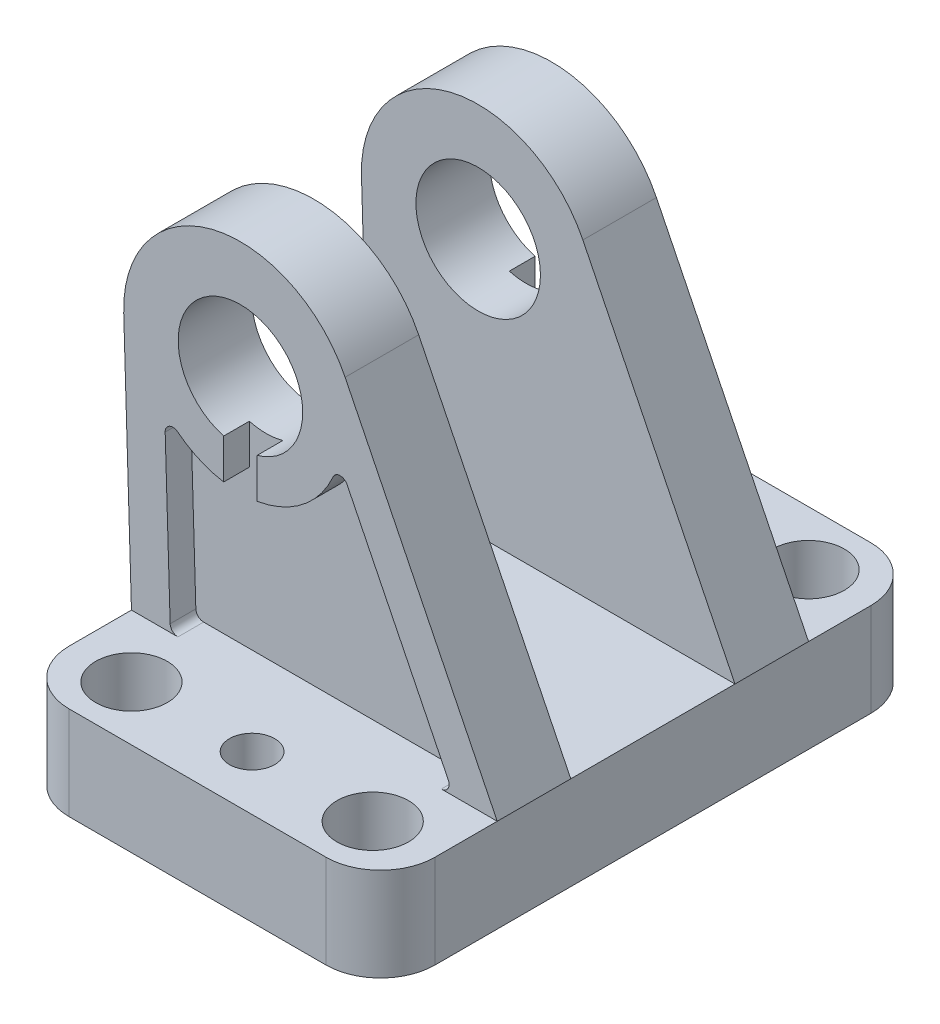
SolidWorks part; units mm, degrees
ref_plane "Front Plane" through (0, 0, 0) normal (0, 0, 1) x (1, 0, 0)
ref_plane "Top Plane" through (0, 0, 0) normal (0, 1, 0) x (1, 0, 0)
ref_plane "Right Plane" through (0, 0, 0) normal (1, 0, 0) x (0, 0, -1)
ref_plane "Plane1" through (0, 0, 0) normal (0, 1, 0) x (1, 0, 0)
sketch "Sketch1" plane through (0, 0, 0) normal (0, 1, 0) x (1, 0, 0)
  line L0 (-16.5, -35) -> (16.5, -35)
  line L1 (23.5, -28) -> (23.5, 28)
  line L2 (16.5, 35) -> (-16.5, 35)
  line L3 (-23.5, 28) -> (-23.5, -28)
  arc A0 (-23.5, -28) -> (-16.5, -35) centre (-16.5, -28) ccw
  arc A1 (16.5, -35) -> (23.5, -28) centre (16.5, -28) ccw
  arc A2 (23.5, 28) -> (16.5, 35) centre (16.5, 28) ccw
  arc A3 (-16.5, 35) -> (-23.5, 28) centre (-16.5, 28) ccw
  circle A4 centre (15.5, 28) radius 4.6
  circle A5 centre (15.5, -28) radius 4.6
  circle A6 centre (0, 28) radius 2.9
  circle A7 centre (0, -28) radius 2.9
  circle A8 centre (-15.5, 28) radius 4.6
  circle A9 centre (-15.5, -28) radius 4.6
extrude "Boss-Extrude1" add sketch "Sketch1" along normal blind 12
ref_plane "Plane2" through (0, 0, 0) normal (0, 1, 0) x (1, 0, 0)
sketch "Sketch2" plane through (0, 0, 0) normal (0, 1, 0) x (1, 0, 0)
  line L0 (-8.006, -23) -> (8.006, -23)
  line L1 (18.5, -18.6106) -> (18.5, 18.6106)
  line L2 (8.006, 23) -> (-8.006, 23)
  line L3 (-18.5, 18.6106) -> (-18.5, -18.6106)
  arc A0 (-18.5, -18.6106) -> (-17.2917, -19.5887) centre (-17.5, -18.6106) ccw
  arc A1 (-17.2917, -19.5887) -> (-8.7866, -22.625) centre (-15.5, -28) cw
  arc A2 (-8.7866, -22.625) -> (-8.006, -23) centre (-8.006, -22) ccw
  arc A3 (8.006, -23) -> (8.7866, -22.625) centre (8.006, -22) ccw
  arc A4 (8.7866, -22.625) -> (17.2917, -19.5887) centre (15.5, -28) cw
  arc A5 (17.2917, -19.5887) -> (18.5, -18.6106) centre (17.5, -18.6106) ccw
  arc A6 (18.5, 18.6106) -> (17.2917, 19.5887) centre (17.5, 18.6106) ccw
  arc A7 (17.2917, 19.5887) -> (8.7866, 22.625) centre (15.5, 28) cw
  arc A8 (8.7866, 22.625) -> (8.006, 23) centre (8.006, 22) ccw
  arc A9 (-8.006, 23) -> (-8.7866, 22.625) centre (-8.006, 22) ccw
  arc A10 (-8.7866, 22.625) -> (-17.2917, 19.5887) centre (-15.5, 28) cw
  arc A11 (-17.2917, 19.5887) -> (-18.5, 18.6106) centre (-17.5, 18.6106) ccw
extrude "Cut-Extrude1" cut sketch "Sketch2" along normal blind 6
ref_plane "Plane3" through (0, 0, 20) normal (0, 0, 1) x (1, 0, 0)
sketch "Sketch3" plane through (0, 0, 20) normal (0, 0, 1) x (1, 0, 0)
  line L0 (-24.493, 44.5425) -> (-23.5, 12)
  line L1 (-23.5, 12) -> (23.5, 12)
  line L2 (23.5, 12) -> (3.9529, 51.6347)
  arc A0 (3.9529, 51.6347) -> (-24.493, 44.5425) centre (-9.5, 45) ccw
  circle A1 centre (-9.5, 45) radius 8
extrude "Boss-Extrude2" add sketch "Sketch3" against normal blind 9.45
ref_plane "Plane4" through (0, 0, 20) normal (0, 0, 1) x (1, 0, 0)
sketch "Sketch4" plane through (0, 0, 20) normal (0, 0, 1) x (1, 0, 0)
  line L0 (-19.1683, 33.9762) -> (-18.5273, 12.9695)
  line L1 (-17.5277, 12) -> (16.3168, 12)
  line L2 (17.2137, 13.4423) -> (4.2119, 39.8054)
  arc A0 (-17.5495, 34.7919) -> (-19.1683, 33.9762) centre (-18.1687, 34.0067) ccw
  arc A1 (-18.5273, 12.9695) -> (-17.5277, 12) centre (-17.5277, 13) ccw
  arc A2 (16.3168, 12) -> (17.2137, 13.4423) centre (16.3168, 13) ccw
  arc A3 (4.2119, 39.8054) -> (2.3997, 39.7657) centre (3.315, 39.3631) ccw
  arc A4 (2.3997, 39.7657) -> (-17.5495, 34.7919) centre (-9.5, 45) cw
extrude "Cut-Extrude2" cut sketch "Sketch4" against normal blind 3.3
ref_plane "Plane5" through (0, 0, -20) normal (0, 0, 1) x (1, 0, 0)
sketch "Sketch5" plane through (0, 0, -20) normal (0, 0, 1) x (1, 0, 0)
  line L0 (-24.493, 44.5425) -> (-23.5, 12)
  line L1 (-23.5, 12) -> (23.5, 12)
  line L2 (23.5, 12) -> (3.9529, 51.6347)
  arc A0 (3.9529, 51.6347) -> (-24.493, 44.5425) centre (-9.5, 45) ccw
  circle A1 centre (-9.5, 45) radius 8
extrude "Boss-Extrude3" add sketch "Sketch5" along normal blind 9.45
ref_plane "Plane6" through (0, 0, -20) normal (0, 0, 1) x (1, 0, 0)
sketch "Sketch6" plane through (0, 0, -20) normal (0, 0, 1) x (1, 0, 0)
  line L0 (-19.1683, 33.9762) -> (-18.5273, 12.9695)
  line L1 (-17.5277, 12) -> (16.3168, 12)
  line L2 (17.2137, 13.4423) -> (4.2119, 39.8054)
  arc A0 (-17.5495, 34.7919) -> (-19.1683, 33.9762) centre (-18.1687, 34.0067) ccw
  arc A1 (-18.5273, 12.9695) -> (-17.5277, 12) centre (-17.5277, 13) ccw
  arc A2 (16.3168, 12) -> (17.2137, 13.4423) centre (16.3168, 13) ccw
  arc A3 (4.2119, 39.8054) -> (2.3997, 39.7657) centre (3.315, 39.3631) ccw
  arc A4 (2.3997, 39.7657) -> (-17.5495, 34.7919) centre (-9.5, 45) cw
extrude "Cut-Extrude3" cut sketch "Sketch6" along normal blind 3.3
ref_plane "Plane7" through (0, 0, 20) normal (0, 0, 1) x (1, 0, 0)
sketch "Sketch7" plane through (0, 0, 20) normal (0, 0, 1) x (1, 0, 0)
  line L0 (-7.35, 30.15) -> (-7.35, 45)
  line L1 (-7.35, 45) -> (-11.65, 45)
  line L2 (-11.65, 45) -> (-11.65, 30.15)
  arc A0 (-11.65, 30.15) -> (-7.35, 30.15) centre (-9.5, 30.15) ccw
extrude "Cut-Extrude4" cut sketch "Sketch7" against normal blind 3.3 and the other way blind 3.3
ref_plane "Plane8" through (0, 0, -20) normal (0, 0, 1) x (1, 0, 0)
sketch "Sketch8" plane through (0, 0, -20) normal (0, 0, 1) x (1, 0, 0)
  line L0 (-7.35, 30.15) -> (-7.35, 45)
  line L1 (-7.35, 45) -> (-11.65, 45)
  line L2 (-11.65, 45) -> (-11.65, 30.15)
  arc A0 (-11.65, 30.15) -> (-7.35, 30.15) centre (-9.5, 30.15) ccw
extrude "Cut-Extrude5" cut sketch "Sketch8" against normal blind 3.3 and the other way blind 3.3
